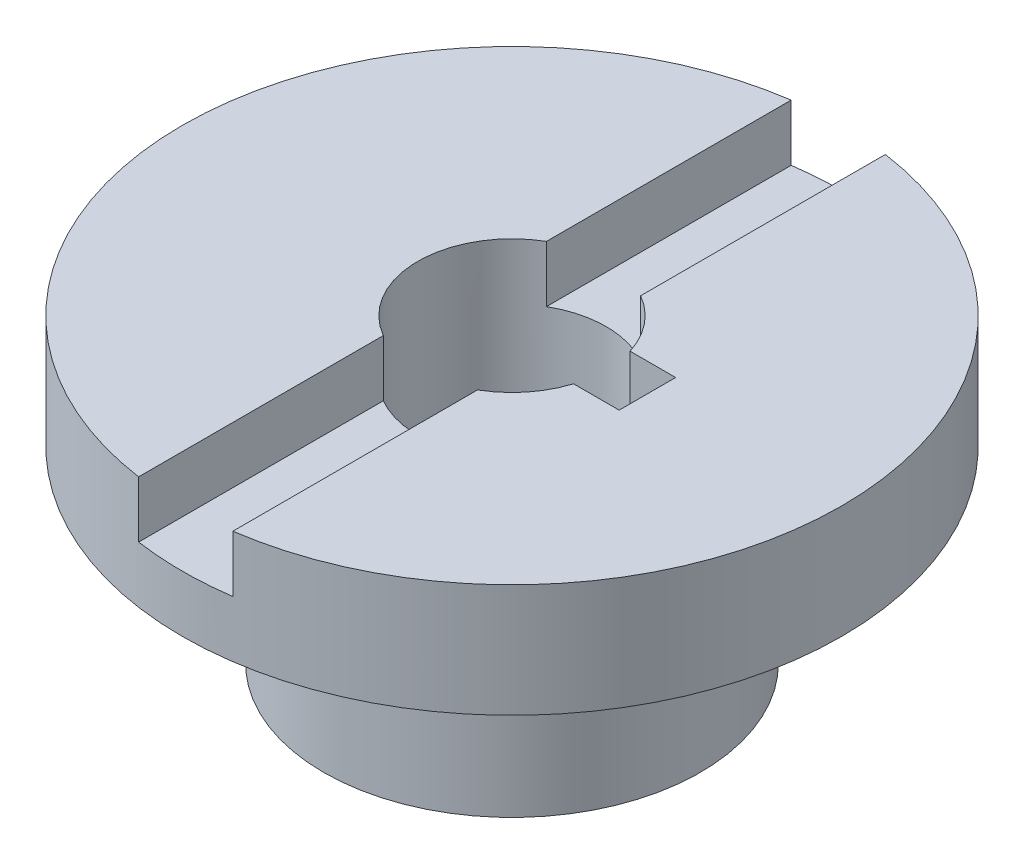
SolidWorks part; units mm, degrees
ref_plane "Front" through (0, 0, 0) normal (0, 0, 1) x (1, 0, 0)
ref_plane "Top" through (0, 0, 0) normal (0, 1, 0) x (1, 0, 0)
ref_plane "Right" through (0, 0, 0) normal (1, 0, 0) x (0, 0, -1)
sketch "Sketch1" plane through (0, 0, 0) normal (0, 1, 0) x (1, 0, 0)
  circle A0 centre (0, 0) radius 10
  circle A1 centre (0, 0) radius 5
  dimension "D1" = 20
  dimension "D2" = 10
extrude "Boss-Extrude1" add sketch "Sketch1" along normal blind 10 contours A0 | A1
sketch "Sketch2" plane through (0, 10, 0) normal (0, 1, 0) x (1, 0, 0)
  circle A0 centre (0, 0) radius 17.5
  dimension "D1" = 35
extrude "Boss-Extrude2" add sketch "Sketch2" along normal blind 6
sketch "Sketch3" plane through (0, 0, 0) normal (0, 0, 1) x (1, 0, 0)
  line L0 (17.5, 16) -> (-17.5, 16) construction
  line L1 (-2.5, 16) -> (2.5, 16)
  line L2 (-2.5, 16) -> (-2.5, 13)
  line L3 (-2.5, 13) -> (2.5, 13)
  line L4 (2.5, 16) -> (2.5, 13)
  line L5 (-10, 10) -> (10, 10) construction
  line L6 (17.5, 10) -> (17.5, 16) construction
  dimension "D1" = 3
  dimension "D2" = 5
  dimension "D3" = 15
extrude "Cut-Extrude1" cut sketch "Sketch3" against normal blind 20 and the other way blind 27
sketch "Sketch4" plane through (0, 10, 0) normal (0, -1, 0) x (1, 0, 0)
  circle A0 centre (0, 0) radius 5
extrude "Cut-Extrude2" cut sketch "Sketch4" against normal blind 20
sketch "Sketch6" plane through (0, 0, 0) normal (0, -1, 0) x (1, 0, 0)
  line L0 (4.6657, 1.5) -> (7.1884, 1.5)
  line L2 (4.6657, 1.5) -> (4.6657, -1.5)
  line L3 (4.6657, -1.5) -> (7.1884, -1.5)
  line L4 (7.1884, 1.5) -> (7.1884, -1.5)
extrude "Cut-Extrude3" cut sketch "Sketch6" against normal blind 20
